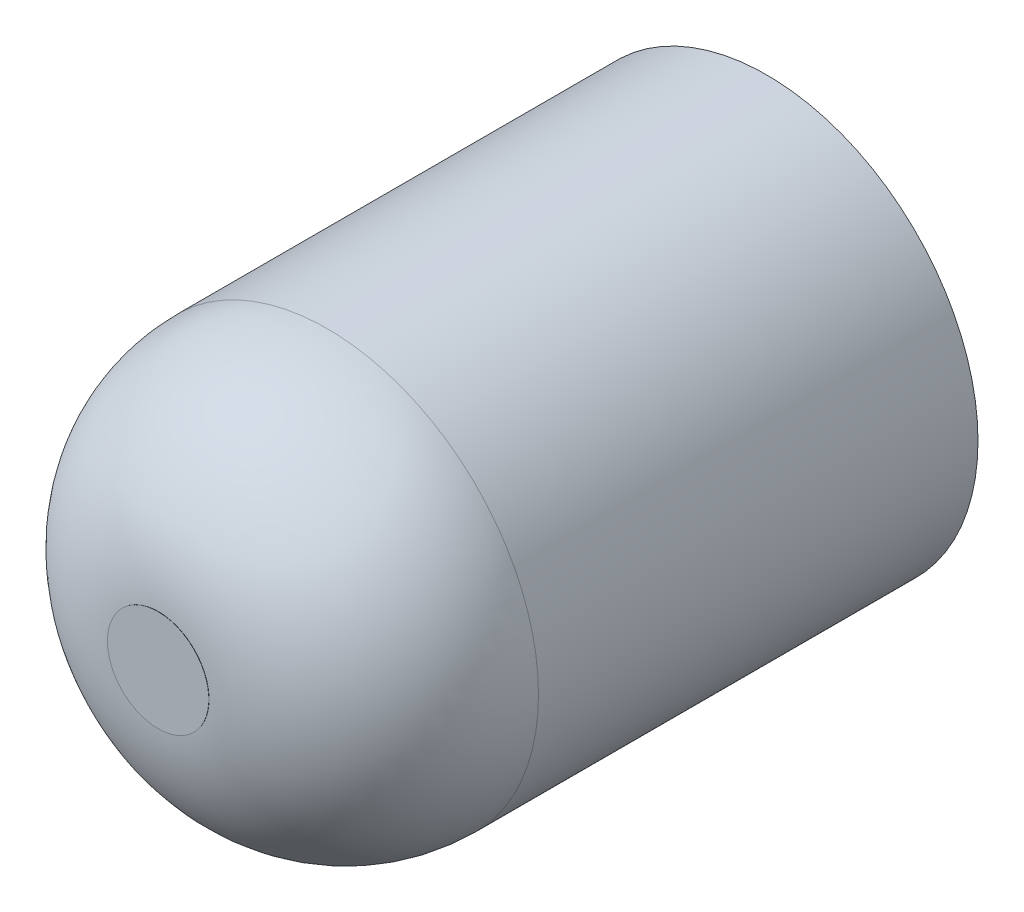
SolidWorks part; units mm, degrees
ref_plane "Alzado" through (0, 0, 0) normal (0, 0, 1) x (1, 0, 0)
ref_plane "Planta" through (0, 0, 0) normal (0, 1, 0) x (1, 0, 0)
ref_plane "Vista lateral" through (0, 0, 0) normal (1, 0, 0) x (0, 0, -1)
sketch "Croquis1" plane through (0, 0, 0) normal (0, 0, 1) x (1, 0, 0)
  line L0 (0, 3) -> (0, 0) construction
  circle A0 centre (0, 0) radius 3
  circle A1 centre (0, 0) radius 9.5
  circle A3 centre (0, 0) radius 9.5
  circle A4 centre (0, 0) radius 14
  dimension "D1" = 6
  dimension "D2" = 19
extrude "Saliente-Extruir1" add sketch "Croquis1" along normal blind 6 contours A1 | A0
sketch "Croquis3" plane through (0, 0, 0) normal (0, 0, -1) x (-1, 0, 0)
  circle A0 centre (0, 0) radius 12.5
extrude "Saliente-Extruir3" add sketch "Croquis3" along normal blind 16 separate body contours A0
fillet "Redondeo1" radius 10 1 edges at (-12.5, 0, -16)
sketch "Croquis5" plane through (0, 0, 0) normal (0, 0, 1) x (1, 0, 0)
  circle A0 centre (0, 0) radius 3 construction
  circle A1 centre (0, 0) radius 3
extrude "Cortar-Extruir1" cut sketch "Croquis5" against normal blind 20
ref_plane "Plano1" through (0, 0, 3) normal (0, 0, -1) x (-1, 0, 0)
mirror "Simetría1" about plane through (0, 0, 3) normal (0, 0, -1) of bodies 104
sketch "Croquis6" plane through (0, 0, 6) normal (0, 0, -1) x (-1, 0, 0)
  circle A0 centre (0, 0) radius 3 construction
  circle A1 centre (0, 0) radius 3
extrude "Saliente-Extruir4" add sketch "Croquis6" along normal blind 22 and the other way blind 16 separate body
sketch "Croquis9" plane through (0, 0, 6) normal (0, 0, -1) x (-1, 0, 0)
  circle A1 centre (0, 0) radius 12.5
  circle A2 centre (0, 0) radius 12.5
  dimension "D1" = 0
extrude "Saliente-Extruir5" add sketch "Croquis9" along normal blind 20
